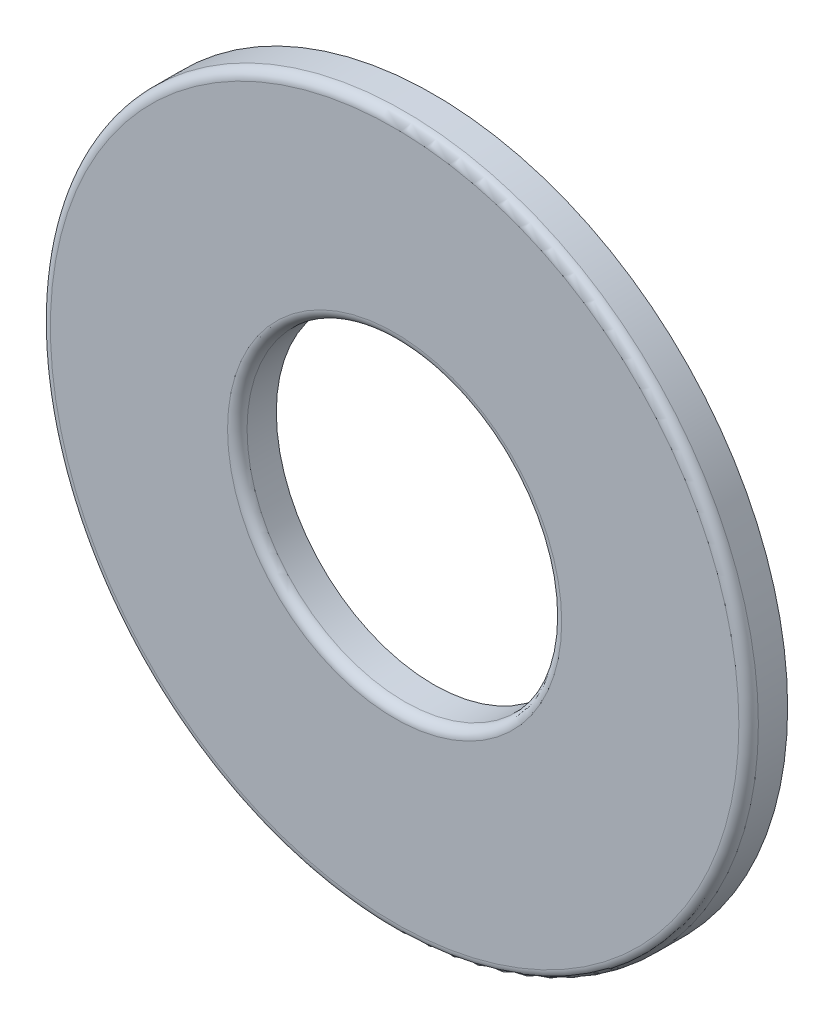
SolidWorks part; units mm, degrees
other "Imported1" parameters "D1"=0.3937, "TH"=1.0287, "Thickness"=1.5748
material "AISI 1020"
ref_plane "Front Plane" through (0, 0, 0) normal (0, 0, 1) x (1, 0, 0)
ref_plane "Top Plane" through (0, 0, 0) normal (0, 1, 0) x (1, 0, 0)
ref_plane "Right Plane" through (0, 0, 0) normal (1, 0, 0) x (0, 0, -1)
sketch "Sketch1" plane through (0, 0, 0) normal (0, 0, 1) x (1, 0, 0)
  line L0 (-14.2875, 0) -> (14.2875, 0) construction
  line L1 (-6.35, 0) -> (6.35, 0) construction
  circle A0 centre (0, 0) radius 6.35 construction
  circle A1 centre (0, 0) radius 14.2875 construction
  point P8 (0, 0)
  point P9 (0, 14.2875)
  point P11 (6.35, 0)
  dimension "ID" = 12.7
  dimension "OD" = 28.575
sketch "Sketch2" plane through (0, 0, 0) normal (1, 0, 0) x (0, 0, -1)
  line L0 (-0.7874, 14.2875) -> (0.7874, 14.2875) construction
  point P2 (0, 14.2875)
sketch "Sketch3" plane through (0, 0, 0) normal (0, 0, 1) x (1, 0, 0)
  circle A0 centre (0, 0) radius 6.35
  circle A1 centre (0, 0) radius 14.2875
extrude "Boss-Extrude1" add sketch "Sketch3" along normal up to vertex (0.7874 mm away) and the other way up to vertex (0.7874 mm away) up to point (0, 14.2875, 0.7874) other way up to point (0, 14.2875, -0.7874)
fillet "Fillet1" radius 0.3937 2 edges at (14.2875, 0, 0.7874) (6.35, 0, 0.7874)
equation "\"D1@Fillet1\"=\"Thickness@Sketch2\"/4"
